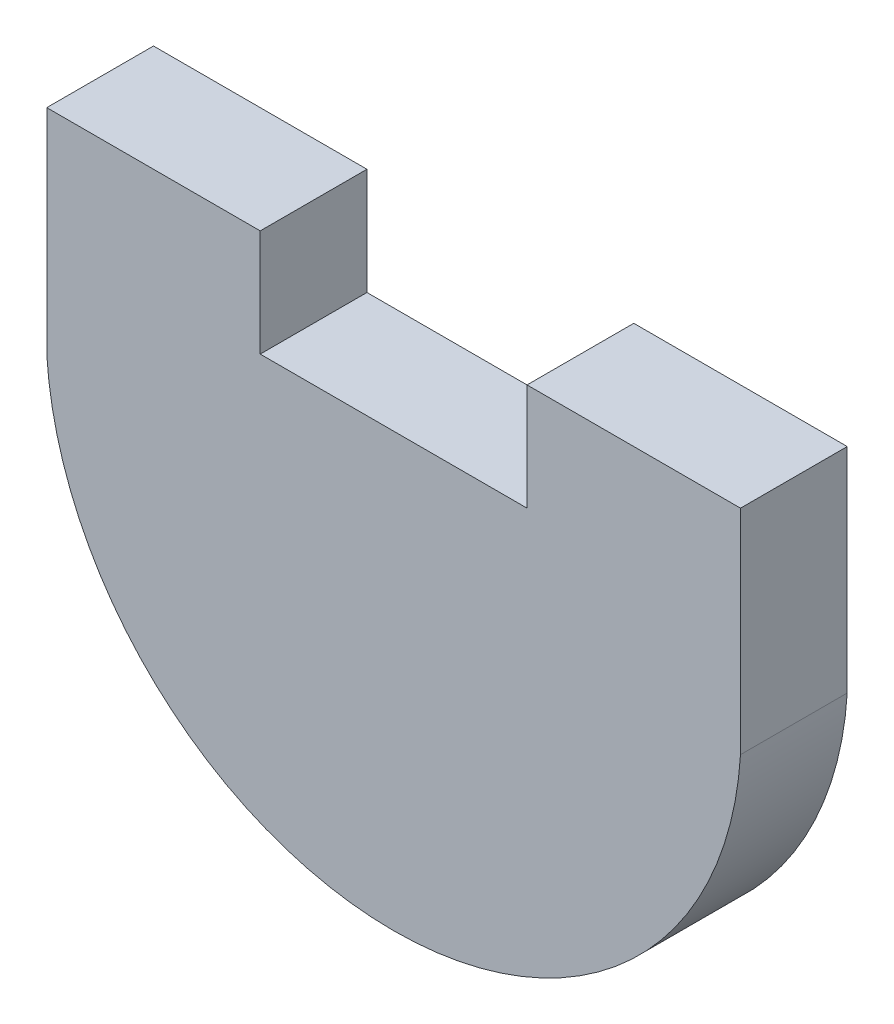
SolidWorks part; units mm, degrees
ref_plane "Front Plane" through (0, 0, 0) normal (0, 0, 1) x (1, 0, 0)
ref_plane "Top Plane" through (0, 0, 0) normal (0, 1, 0) x (1, 0, 0)
ref_plane "Right Plane" through (0, 0, 0) normal (1, 0, 0) x (0, 0, -1)
sketch "Sketch1" plane through (0, 0, 0) normal (0, 0, 1) x (1, 0, 0)
  line L1 (-16.51, 12.7) -> (16.51, 12.7)
  line L2 (-16.51, 12.7) -> (-16.51, 2.54)
  line L4 (16.51, 12.7) -> (16.51, 2.54)
  line L5 (-16.51, 12.7) -> (16.51, -12.7) construction
  line L6 (-16.51, -12.7) -> (16.51, 12.7) construction
  arc A0 (-16.51, 2.54) -> (16.51, 2.54) centre (0, 3.5672) ccw
  point P0 (0, 0)
  dimension "D1" = 25.4
  dimension "D2" = 33.02
extrude "Boss-Extrude1" add sketch "Sketch1" along normal blind 5.08
sketch "Sketch2" plane through (0, 0, 5.08) normal (0, 0, 1) x (1, 0, 0)
  line L0 (16.51, 12.7) -> (-16.51, 12.7) construction
  line L1 (-6.35, 12.7) -> (6.35, 12.7)
  line L2 (-6.35, 12.7) -> (-6.35, 7.62)
  line L3 (-6.35, 7.62) -> (6.35, 7.62)
  line L4 (6.35, 12.7) -> (6.35, 7.62)
  line L5 (16.51, 2.54) -> (16.51, 12.7) construction
  line L6 (-16.51, 12.7) -> (-16.51, 2.54) construction
  dimension "D1" = 5.08
  dimension "D2" = 12.7
  dimension "D3" = 10.16
  dimension "D4" = 10.16
extrude "Cut-Extrude1" cut sketch "Sketch2" against normal up to surface (5.08 mm away) up to face at (0, 3.7413, 0)
